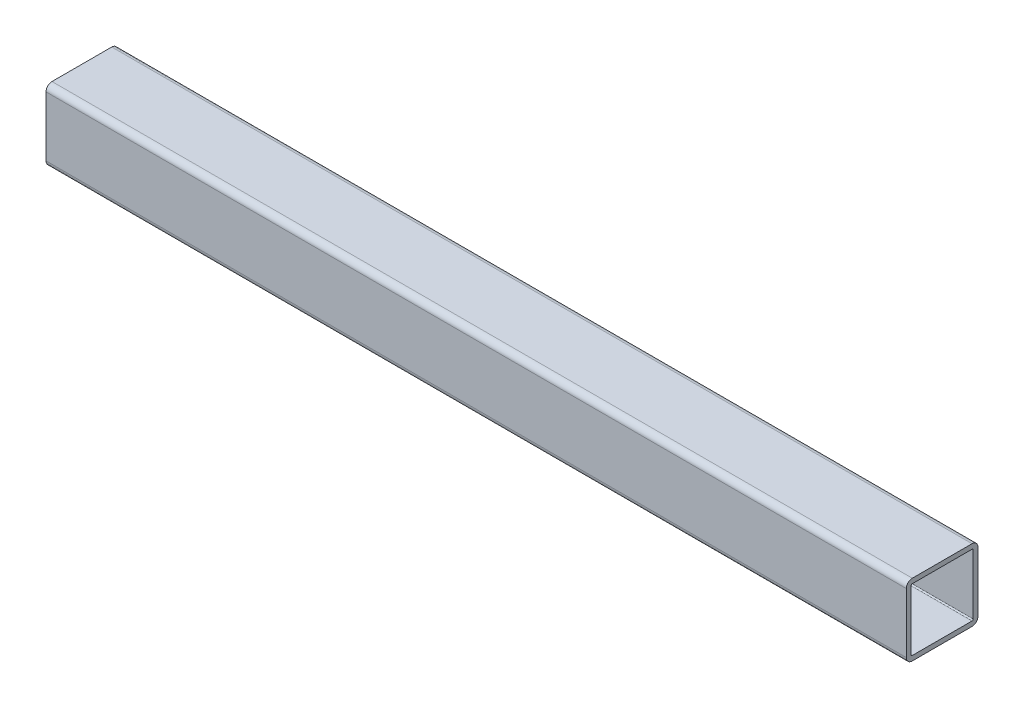
SolidWorks part; units mm, degrees
ref_plane "Front Plane" through (0, 0, 0) normal (0, 0, 1) x (1, 0, 0)
ref_plane "Top Plane" through (0, 0, 0) normal (0, 1, 0) x (1, 0, 0)
ref_plane "Right Plane" through (0, 0, 0) normal (1, 0, 0) x (0, 0, -1)
sketch "Sketch1" plane through (0, 0, 0) normal (1, 0, 0) x (0, 0, -1)
  line L1 (-15.875, 19.05) -> (15.875, 19.05)
  line L2 (-19.05, 15.875) -> (-19.05, -15.875)
  line L3 (-15.875, -19.05) -> (15.875, -19.05)
  line L4 (19.05, 15.875) -> (19.05, -15.875)
  line L5 (-19.05, 19.05) -> (19.05, -19.05) construction
  line L6 (-19.05, -19.05) -> (19.05, 19.05) construction
  arc A0 (-19.05, -15.875) -> (-15.875, -19.05) centre (-15.875, -15.875) ccw
  arc A1 (15.875, -19.05) -> (19.05, -15.875) centre (15.875, -15.875) ccw
  arc A2 (19.05, 15.875) -> (15.875, 19.05) centre (15.875, 15.875) ccw
  arc A3 (-15.875, 19.05) -> (-19.05, 15.875) centre (-15.875, 15.875) ccw
  point P0 (0, 0)
  dimension "D3" = 3.175
  dimension "D1" = 38.1
  dimension "D2" = 38.1
extrude "Extrude-Thin1" add sketch "Sketch1" along normal mid plane 457.2 thin
sketch "Sketch4" plane through (0, -19.05, 0) normal (0, -1, 0) x (1, 0, 0)
  line L0 (228.6, 0) -> (-228.6, 0) construction
  line L1 (228.6, 15.875) -> (228.6, -15.875) construction
  line L2 (19.05, 15.875) -> (19.05, -15.875) construction
  line L3 (228.6, 15.875) -> (-228.6, 15.875) construction
  line L4 (228.6, -15.875) -> (-228.6, -15.875) construction
  line L5 (177.8, 15.875) -> (177.8, -15.875) construction
  line L6 (-228.6, 15.875) -> (-228.6, -15.875) construction
  line L7 (-209.55, 15.875) -> (-209.55, -15.875) construction
  dimension "D1" = 50.8
  dimension "D2" = 209.55
  dimension "D3" = 19.05
